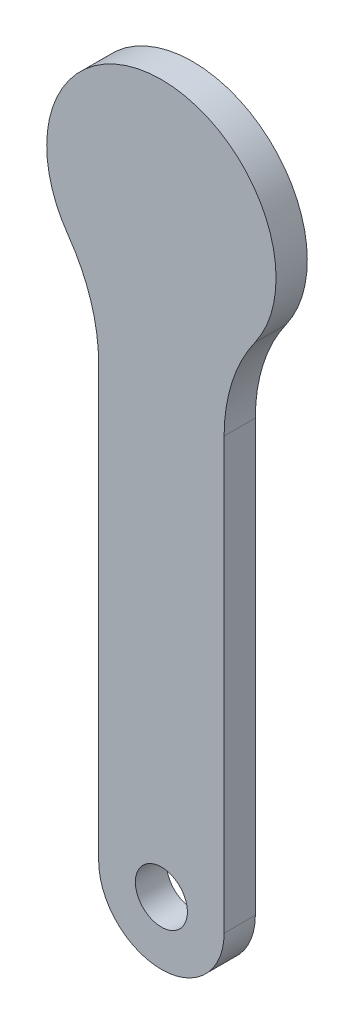
SolidWorks part; units mm, degrees
ref_plane "Спереди" through (0, 0, 0) normal (0, 0, 1) x (1, 0, 0)
ref_plane "Сверху" through (0, 0, 0) normal (0, 1, 0) x (1, 0, 0)
ref_plane "Справа" through (0, 0, 0) normal (1, 0, 0) x (0, 0, -1)
other "Configuration Table"
sketch "Sketch1" plane through (0, 0, 0) normal (0, 0, 1) x (1, 0, 0)
  line L0 (0, -11.0148) -> (0, -57.1777) construction
  line L1 (6.0251, -15.6362) -> (6.0251, -57)
  line L2 (-6.0251, -15.6362) -> (-6.0251, -57)
  circle A0 centre (0, 0) radius 11.0148 construction
  arc A1 (6.0251, -57) -> (0, -63.0251) centre (0, -57) cw
  arc A2 (6.0251, -15.6362) -> (8.9788, -6.3802) centre (22.0049, -15.6362) cw
  arc A3 (-6.0251, -15.6362) -> (-8.9788, -6.3802) centre (-22.0049, -15.6362) ccw
  arc A4 (-6.0251, -57) -> (0, -63.0251) centre (0, -57) ccw
  circle A5 centre (0, -57) radius 2.5
  arc A6 (-8.9788, -6.3802) -> (8.9788, -6.3802) centre (0, 0) cw
  point P7 (0, -65.8549)
  point P8 (0, -59.3782)
  point P12 (-8.9788, -6.3802)
  point P13 (0, 0)
  dimension "D1" = 5
  dimension "D2" = 57
extrude "Boss-Extrude1" add sketch "Sketch1" along normal blind 3
